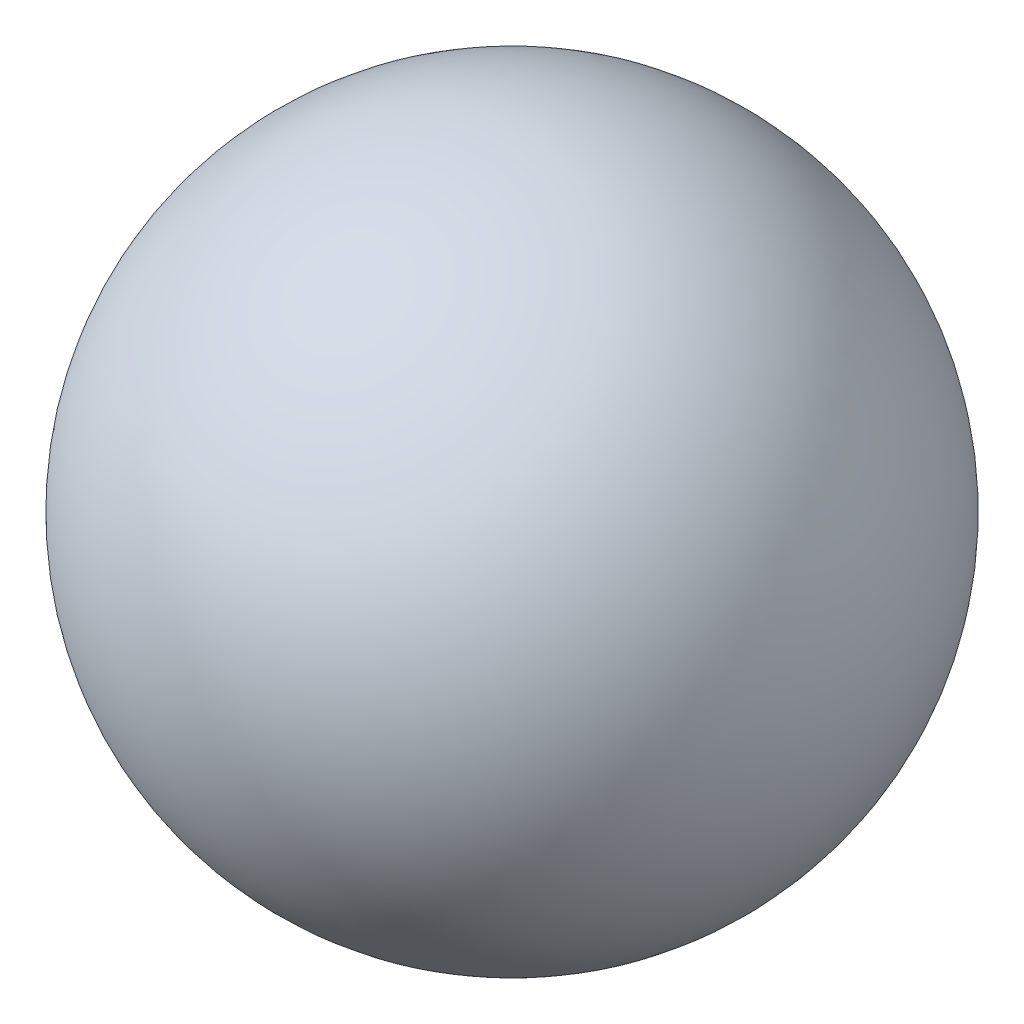
SolidWorks part; units mm, degrees
ref_plane "Ön Düzlem" through (0, 0, 0) normal (0, 0, 1) x (1, 0, 0)
ref_plane "Üst Düzlem" through (0, 0, 0) normal (0, 1, 0) x (1, 0, 0)
ref_plane "Sağ Düzlem" through (0, 0, 0) normal (1, 0, 0) x (0, 0, -1)
sketch "Çizim2" plane through (0, 0, 0) normal (0, 0, 1) x (1, 0, 0)
  line L0 (0, 52.4895) -> (0, -50.607) construction
  line L1 (0, 40) -> (0, -40)
  arc A0 (0, -40) -> (0, 40) centre (0, 0) ccw
  dimension "D1" = 80
revolve "Döndür5" add sketch "Çizim2" angle 360 about L0
